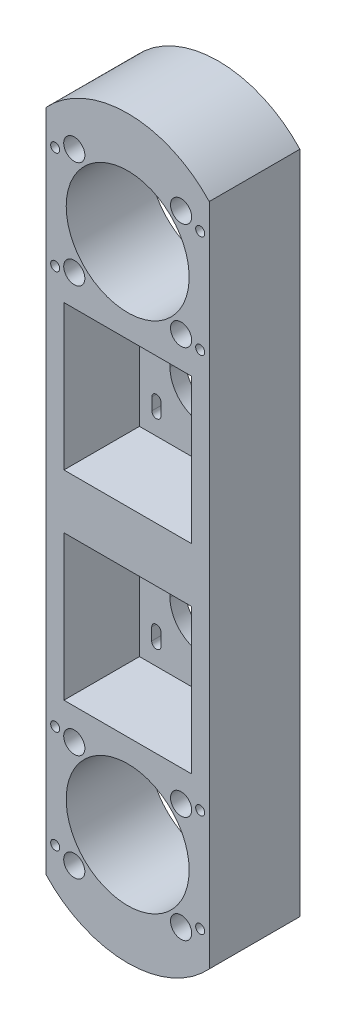
SolidWorks part; units mm, degrees
ref_plane "前视基准面" through (0, 0, 0) normal (0, 0, 1) x (1, 0, 0)
ref_plane "上视基准面" through (0, 0, 0) normal (0, 1, 0) x (1, 0, 0)
ref_plane "右视基准面" through (0, 0, 0) normal (1, 0, 0) x (0, 0, -1)
sketch "草图1" plane through (0, 0, 0) normal (0, 0, 1) x (1, 0, 0)
  line L1 (-27, 110) -> (27, 110)
  line L2 (-27, 110) -> (-27, -110)
  line L3 (-27, -110) -> (27, -110)
  line L4 (27, 110) -> (27, -110)
  line L5 (0, -110) -> (0, 110) construction
  line L6 (-27, 0) -> (27, 0) construction
  point P0 (0, 0)
  dimension "D1" = 220
  dimension "D2" = 54
extrude "凸台-拉伸1" add sketch "草图1" along normal blind 30
sketch "草图2" plane through (0, 0, 30) normal (0, 0, 1) x (1, 0, 0)
  line L0 (0, 99) -> (0, -113.7312) construction
  line L1 (-21.1, 57) -> (21.1, 57)
  line L2 (-21.1, 57) -> (-21.1, 9)
  line L3 (-21.1, 9) -> (21.1, 9)
  line L4 (21.1, 57) -> (21.1, 9)
  line L5 (0, 9) -> (0, 57) construction
  line L6 (-21.1, 33) -> (21.1, 33) construction
  line L7 (27, 110) -> (-27, 110) construction
  line L12 (0, 53) -> (0, 95) construction
  line L13 (-21, 85) -> (21, 85) construction
  point P0 (0, 33)
  point P6 (0, 85)
  dimension "D1" = 48
  dimension "D2" = 42.2
  dimension "D3" = 25
  dimension "D4" = 52
extrude "切除-拉伸1" cut sketch "草图2" against normal offset from surface (25 mm away) 5 up to face at (0, 0, 0)
sketch "草图3" plane through (0, 0, 30) normal (0, 0, -1) x (-1, 0, 0)
  line L0 (0, 105.3067) -> (0, -113.1294) construction
  line L1 (-21.1, -9) -> (21.1, -9)
  line L2 (-21.1, -9) -> (-21.1, -57)
  line L3 (-21.1, -57) -> (21.1, -57)
  line L4 (21.1, -9) -> (21.1, -57)
  line L5 (0, -57) -> (0, -9) construction
  line L6 (-21.1, -33) -> (21.1, -33) construction
  line L7 (27, -110) -> (-27, -110) construction
  line L12 (0, -95) -> (0, -53) construction
  line L13 (-21, -85) -> (21, -85) construction
  point P0 (0, -33)
  point P6 (0, -85)
  dimension "D1" = 48
  dimension "D2" = 42.2
  dimension "D3" = 25
  dimension "D4" = 52
extrude "切除-拉伸2" cut sketch "草图3" along normal offset from surface (25 mm away) 5 up to face at (0, 0, 0)
sketch "草图4" plane through (0, 0, 5) normal (0, 0, 1) x (1, 0, 0)
  line L0 (0, 33) -> (40.432, 33) construction
  line L1 (0, 0) -> (0, -107.9783) construction
  line L2 (-21.1, 57) -> (21.1, 57) construction
  line L3 (-21.1, 9) -> (21.1, 57) construction
  line L4 (21.1, 57) -> (21.1, 9) construction
  line L5 (-21.1, 57) -> (21.1, 9) construction
  line L6 (0, 35) -> (0, 31) construction
  line L7 (11, 35) -> (11, 31)
  line L8 (-11, 35) -> (-11, 31)
  line L9 (-15.5, 50.5) -> (-15.5, 46.5) construction
  line L10 (-14, 50.5) -> (-14, 46.5)
  line L11 (-17, 50.5) -> (-17, 46.5)
  line L12 (0, 33) -> (0, 63.0659) construction
  line L14 (15.5, 50.5) -> (15.5, 46.5) construction
  line L15 (14, 50.5) -> (14, 46.5)
  line L16 (17, 50.5) -> (17, 46.5)
  line L17 (15.5, 15.5) -> (15.5, 19.5) construction
  line L18 (14, 15.5) -> (14, 19.5)
  line L19 (17, 15.5) -> (17, 19.5)
  line L20 (-15.5, 15.5) -> (-15.5, 19.5) construction
  line L21 (-14, 15.5) -> (-14, 19.5)
  line L22 (-17, 15.5) -> (-17, 19.5)
  arc A17 (11, 35) -> (-11, 35) centre (0, 35) ccw
  arc A18 (-11, 31) -> (11, 31) centre (0, 31) ccw
  arc A19 (-14, 50.5) -> (-17, 50.5) centre (-15.5, 50.5) ccw
  arc A20 (-17, 46.5) -> (-14, 46.5) centre (-15.5, 46.5) ccw
  arc A21 (14, 50.5) -> (17, 50.5) centre (15.5, 50.5) cw
  arc A22 (17, 46.5) -> (14, 46.5) centre (15.5, 46.5) cw
  arc A23 (14, 15.5) -> (17, 15.5) centre (15.5, 15.5) ccw
  arc A24 (17, 19.5) -> (14, 19.5) centre (15.5, 19.5) ccw
  arc A25 (-14, 15.5) -> (-17, 15.5) centre (-15.5, 15.5) cw
  arc A26 (-17, 19.5) -> (-14, 19.5) centre (-15.5, 19.5) cw
  point P12 (0, 33)
  point P15 (0, 33)
  point P22 (-15.5, 48.5)
  point P32 (15.5, 48.5)
  point P39 (15.5, 17.5)
  point P46 (-15.5, 17.5)
  dimension "D1" = 4
  dimension "D4" = 4
  dimension "D3" = 1.5
  dimension "D6" = 11
  dimension "D2" = 15.5
  dimension "D5" = 15.5
extrude "切除-拉伸3" cut sketch "草图4" against normal through all
sketch "草图18" plane through (0, 0, 0) normal (0, 0, 1) x (1, 0, 0)
  line L1 (-21.35, -63.65) -> (21.35, -63.65)
  line L2 (-21.35, -63.65) -> (-21.35, -106.35)
  line L3 (-21.35, -106.35) -> (21.35, -106.35)
  line L4 (21.35, -63.65) -> (21.35, -106.35)
  line L5 (0, -106.35) -> (0, -63.65) construction
  line L6 (-21.35, -85) -> (21.35, -85) construction
  point P0 (0, -85)
  dimension "D1" = 42.7
  dimension "D2" = 42.7
sketch "草图26" plane through (0, 0, 5) normal (0, 0, 1) x (1, 0, 0)
  line L0 (-21.1, -57) -> (21.1, -9) construction
  line L1 (-21.1, -9) -> (21.1, -57) construction
  line L2 (0, -31) -> (0, -35) construction
  line L3 (21.1, -33) -> (-21.1, -33) construction
  line L4 (0, 99) -> (0, -113.7312) construction
  line L5 (11, -31) -> (11, -35)
  line L6 (-11, -31) -> (-11, -35)
  line L7 (-15.5, -15.5) -> (-15.5, -19.5) construction
  line L8 (-13.95, -15.5) -> (-13.95, -19.5)
  line L9 (-17.05, -15.5) -> (-17.05, -19.5)
  line L10 (0, -33) -> (45.7169, -33) construction
  line L11 (0, -33) -> (0, -41.2979) construction
  line L12 (-15.5, -50.5) -> (-15.5, -46.5) construction
  line L13 (-13.95, -50.5) -> (-13.95, -46.5)
  line L14 (-17.05, -50.5) -> (-17.05, -46.5)
  line L15 (15.5, -50.5) -> (15.5, -46.5) construction
  line L16 (13.95, -50.5) -> (13.95, -46.5)
  line L17 (17.05, -50.5) -> (17.05, -46.5)
  line L18 (15.5, -15.5) -> (15.5, -19.5) construction
  line L19 (13.95, -15.5) -> (13.95, -19.5)
  line L20 (17.05, -15.5) -> (17.05, -19.5)
  arc A0 (11, -31) -> (-11, -31) centre (0, -31) ccw
  arc A1 (-11, -35) -> (11, -35) centre (0, -35) ccw
  arc A2 (-13.95, -15.5) -> (-17.05, -15.5) centre (-15.5, -15.5) ccw
  arc A3 (-17.05, -19.5) -> (-13.95, -19.5) centre (-15.5, -19.5) ccw
  arc A4 (-13.95, -50.5) -> (-17.05, -50.5) centre (-15.5, -50.5) cw
  arc A5 (-17.05, -46.5) -> (-13.95, -46.5) centre (-15.5, -46.5) cw
  arc A6 (13.95, -50.5) -> (17.05, -50.5) centre (15.5, -50.5) ccw
  arc A7 (17.05, -46.5) -> (13.95, -46.5) centre (15.5, -46.5) ccw
  arc A8 (13.95, -15.5) -> (17.05, -15.5) centre (15.5, -15.5) cw
  arc A9 (17.05, -19.5) -> (13.95, -19.5) centre (15.5, -19.5) cw
  point P8 (0, -33)
  point P16 (0, -33)
  point P23 (-15.5, -17.5)
  point P34 (-15.5, -48.5)
  point P41 (15.5, -48.5)
  point P48 (15.5, -17.5)
  dimension "D2" = 11
  dimension "D4" = 1.55
  dimension "D1" = 4
  dimension "D3" = 4
  dimension "D5" = 15.5
  dimension "D6" = 15.5
extrude "切除-拉伸13" cut sketch "草图26" against normal through all
extrude "切除-拉伸9" cut sketch "草图18" along normal blind 2.5
sketch "草图9" plane through (0, 0, 2.5) normal (0, 0, 1) x (1, 0, 0)
  line L0 (21.35, -85) -> (-21.35, -85) construction
  line L3 (0, -63.65) -> (0, -106.35) construction
  line L6 (-21.35, -63.65) -> (21.35, -63.65) construction
  line L8 (21.35, -106.35) -> (-21.35, -106.35) construction
  line L9 (-21.35, -106.35) -> (-21.35, -63.65) construction
  line L10 (21.35, -63.65) -> (21.35, -106.35) construction
  circle A1 centre (0, -85) radius 20.35
  circle A2 centre (-17.6777, -67.3223) radius 2.1
  circle A3 centre (17.6777, -67.3223) radius 2.1
  circle A4 centre (17.6777, -102.6777) radius 2.1
  circle A5 centre (-17.6777, -102.6777) radius 2.1
  point P26 (0, -85)
  dimension "D1" = 40.7
  dimension "D2" = 4.2
  dimension "D3" = 25
  dimension "D5" = 4
extrude "切除-拉伸4" cut sketch "草图9" along normal through all
sketch "草图16" plane through (0, 0, 0) normal (0, 0, 1) x (1, 0, 0)
  line L1 (-21.35, 106.35) -> (21.35, 106.35)
  line L2 (-21.35, 106.35) -> (-21.35, 63.65)
  line L3 (-21.35, 63.65) -> (21.35, 63.65)
  line L4 (21.35, 106.35) -> (21.35, 63.65)
  line L5 (0, 63.65) -> (0, 106.35) construction
  line L6 (-21.35, 85) -> (21.35, 85) construction
  point P0 (0, 85)
  dimension "D1" = 42.7
  dimension "D2" = 42.7
extrude "切除-拉伸7" cut sketch "草图16" along normal blind 2.5
sketch "草图13" plane through (0, 0, 2.5) normal (0, 0, -1) x (-1, 0, 0)
  line L0 (21.35, 85) -> (-21.35, 85) construction
  line L1 (-27, 110) -> (27, 110) construction
  line L2 (0, 85) -> (0, 93.445) construction
  line L3 (21.35, 63.65) -> (21.35, 106.35) construction
  line L4 (27, 110) -> (27, -110) construction
  line L5 (-27, -110) -> (-27, 110) construction
  line L6 (-21.35, 106.35) -> (-21.35, 63.65) construction
  line L7 (0, 106.35) -> (0, 63.65) construction
  line L8 (21.35, 106.35) -> (-21.35, 106.35) construction
  line L9 (-21.35, 63.65) -> (21.35, 63.65) construction
  circle A0 centre (0, 85) radius 20.35
  circle A1 centre (-17.6777, 102.6777) radius 2.1
  circle A2 centre (17.6777, 102.6777) radius 2.1
  circle A3 centre (17.6777, 67.3223) radius 2.1
  circle A4 centre (-17.6777, 67.3223) radius 2.1
  point P25 (0, 85)
  dimension "D1" = 40.7
  dimension "D2" = 4.2
  dimension "D3" = 25
  dimension "D6" = 25
  dimension "D5" = 4
extrude "切除-拉伸6" cut sketch "草图13" against normal through all
sketch "草图15" plane through (0, 0, 0) normal (0, 0, -1) x (-1, 0, 0)
  line L0 (-27, 110) -> (27, 110) construction
  line L1 (-27, 110) -> (27, 110)
  arc A0 (-27, 110) -> (27, 110) centre (0, 85) cw
extrude "凸台-拉伸3" add sketch "草图15" against normal up to surface (30 mm away) up to face at (15.5777, 67.3223, 30)
sketch "草图17" plane through (0, 0, 0) normal (0, 0, -1) x (-1, 0, 0)
  line L0 (0, 99) -> (0, -113.7312) construction
  circle A0 centre (-24, 100) radius 1.5
  circle A1 centre (24, 100) radius 1.5
  circle A2 centre (24, 66) radius 1.5
  circle A3 centre (-24, 66) radius 1.5
  dimension "D1" = 3
  dimension "D2" = 10
  dimension "D3" = 24
  dimension "D4" = 2
  dimension "D5" = 2
extrude "切除-拉伸8" cut sketch "草图17" against normal up to next
fillet "圆角1" [suppressed] radius 10
sketch "草图21" plane through (0, 0, 30) normal (0, 0, 1) x (1, 0, 0)
  circle A0 centre (-17.6777, 102.6777) radius 3.5
  circle A1 centre (17.6777, 102.6777) radius 3.5
  circle A2 centre (17.6777, 67.3223) radius 3.5
  circle A3 centre (-17.6777, 67.3223) radius 3.5
  point P12 (0, 85)
  dimension "D1" = 7
  dimension "D2" = 4
extrude "切除-拉伸11" cut sketch "草图21" against normal blind 7.5 and the other way through all
sketch "草图28" plane through (0, 0, 30) normal (0, 0, 1) x (1, 0, 0)
  line L0 (0, 99) -> (0, -113.7312) construction
  line L1 (-27, -110) -> (27, -110) construction
  line L2 (-27, -110) -> (27, -110)
  arc A0 (-27, -110) -> (27, -110) centre (0, -84.9952) ccw
  dimension "D1" = 36.8
extrude "凸台-拉伸4" add sketch "草图28" against normal up to surface (30 mm away) up to face at (22.5, 66, 0)
sketch "草图29" plane through (0, 0, 30) normal (0, 0, 1) x (1, 0, 0)
  circle A0 centre (-17.6777, -67.3223) radius 3.5
  circle A1 centre (17.6777, -67.3223) radius 3.5
  circle A2 centre (17.6777, -102.6777) radius 3.5
  circle A3 centre (-17.6777, -102.6777) radius 3.5
  point P12 (0, -85)
  dimension "D1" = 7
  dimension "D2" = 4
extrude "切除-拉伸15" cut sketch "草图29" against normal blind 7.5
sketch "草图30" plane through (0, 0, 0) normal (0, 0, -1) x (-1, 0, 0)
  line L0 (0, 99) -> (0, -113.7312) construction
  circle A0 centre (-24, -100) radius 1.5
  circle A1 centre (-24, -66) radius 1.5
  circle A2 centre (24, -66) radius 1.5
  circle A3 centre (24, -100) radius 1.5
  dimension "D1" = 3
  dimension "D2" = 10
  dimension "D3" = 24
  dimension "D4" = 2
  dimension "D5" = 2
extrude "切除-拉伸16" cut sketch "草图30" against normal up to next
sketch "草图31" plane through (0, 0, 0) normal (0, 0, -1) x (-1, 0, 0)
  line L1 (-33.0543, -60.0516) -> (30.9302, -60.0516)
  line L2 (-33.0543, -60.0516) -> (-33.0543, -107.6777)
  line L3 (-33.0543, -107.6777) -> (30.9302, -107.6777)
  line L4 (30.9302, -60.0516) -> (30.9302, -107.6777)
